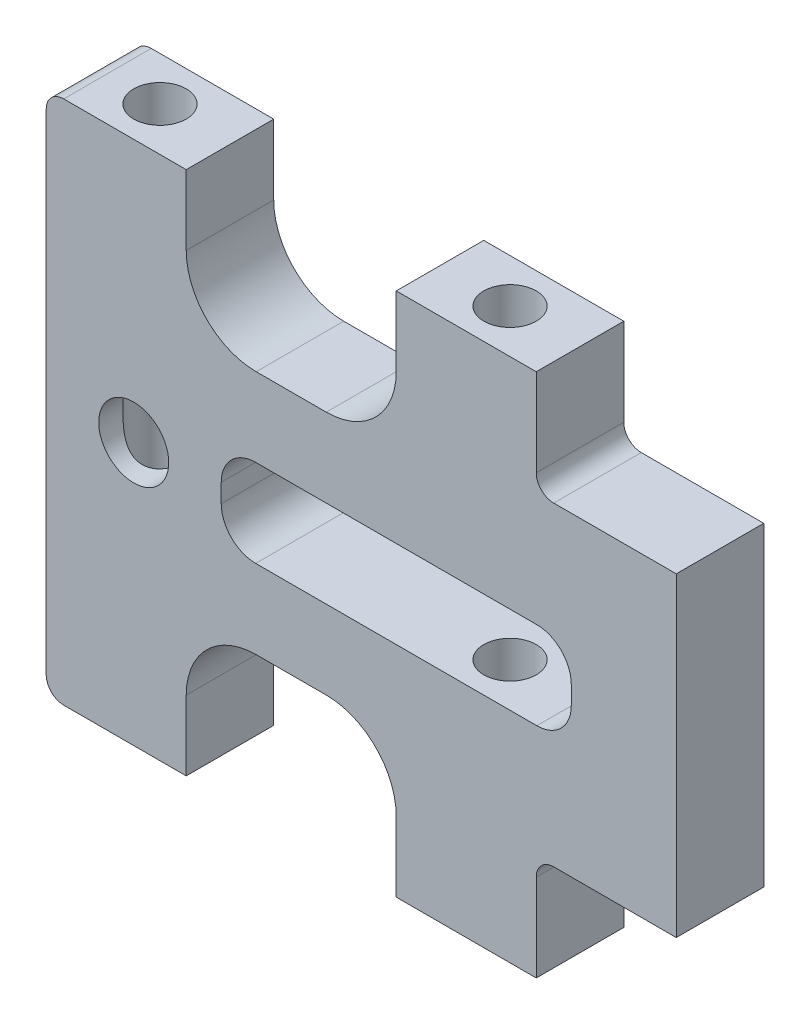
SolidWorks part; units mm, degrees
ref_plane "Front Plane" through (0, 0, 0) normal (0, 0, 1) x (1, 0, 0)
ref_plane "Top Plane" through (0, 0, 0) normal (0, 1, 0) x (1, 0, 0)
ref_plane "Right Plane" through (0, 0, 0) normal (1, 0, 0) x (0, 0, -1)
sketch "Sketch1" plane through (0, 0, 0) normal (0, 0, 1) x (1, 0, 0)
  line L1 (1, 0) -> (35, 0)
  line L2 (0, 1) -> (0, 7)
  line L3 (1, 30) -> (35, 30)
  line L4 (36, 1) -> (36, 29)
  line L7 (0, 7) -> (0, 29)
  line L9 (11.9675, 12.5) -> (28.0325, 12.5)
  line L10 (10, 14.4675) -> (10, 15.5325)
  line L11 (11.9675, 17.5) -> (28.0325, 17.5)
  line L12 (30, 14.4675) -> (30, 15.5325)
  line L13 (10, 12.5) -> (30, 17.5) construction
  line L14 (10, 17.5) -> (30, 12.5) construction
  circle A2 centre (5, 15) radius 2
  arc A3 (30, 15.5325) -> (28.0325, 17.5) centre (28.0325, 15.5325) ccw
  arc A4 (30, 14.4675) -> (28.0325, 12.5) centre (28.0325, 14.4675) cw
  arc A5 (10, 14.4675) -> (11.9675, 12.5) centre (11.9675, 14.4675) ccw
  arc A6 (10, 15.5325) -> (11.9675, 17.5) centre (11.9675, 15.5325) cw
  arc A7 (36, 29) -> (35, 30) centre (35, 29) ccw
  arc A8 (35, 0) -> (36, 1) centre (35, 1) ccw
  arc A10 (1, 0) -> (0, 1) centre (1, 1) cw
  arc A12 (0, 29) -> (1, 30) centre (1, 29) cw
  point P5 (0, 0)
  point P13 (10, 8)
  point P16 (20, 15)
  point P21 (0, 0)
  point P40 (0, 8)
  point P43 (0, 0)
  point P46 (0, 22)
  dimension "D6" = 5
  dimension "D8" = 1.9675
  dimension "D9" = 1
  dimension "D3" = 10
  dimension "D7" = 5
  dimension "D10" = 15
  dimension "D11" = 30
  dimension "D12" = 36
extrude "Boss-Extrude1" add sketch "Sketch1" along normal blind 5
sketch "Sketch2" plane through (0, 30, 0) normal (0, 1, 0) x (1, 0, 0)
  line L0 (0, -5) -> (0, 0) construction
  circle A0 centre (4, -2.5) radius 1.5
  circle A1 centre (24, -2.5) radius 1.5
  dimension "D1" = 4
  dimension "D2" = 20
extrude "Cut-Extrude1" cut sketch "Sketch2" against normal through all
sketch "Sketch3" plane through (0, 0, 5) normal (0, 0, 1) x (1, 0, 0)
  line L0 (28, 30) -> (28, 25)
  line L1 (35, 30) -> (1, 30) construction
  line L3 (44, 23) -> (44, 7)
  line L4 (43, 6) -> (29, 6)
  line L5 (28, 5) -> (28, 0)
  line L6 (1, 0) -> (35, 0) construction
  line L7 (28, 30) -> (56.7553, 30)
  line L8 (56.7553, 30) -> (56.7553, 0)
  line L9 (56.7553, 0) -> (28, 0)
  line L10 (43, 24) -> (29, 24)
  line L11 (8, 30) -> (8, 26)
  line L12 (12, 22) -> (16, 22)
  line L13 (20, 26) -> (20, 30)
  line L14 (0, 29) -> (0, 1) construction
  line L15 (8, 30) -> (20, 30)
  line L16 (0, 29) -> (0, 1) construction
  line L17 (8, 0) -> (8, 4)
  line L18 (12, 8) -> (16, 8)
  line L19 (20, 4) -> (20, 0)
  line L20 (8, 0) -> (20, 0)
  arc A0 (28, 25) -> (29, 24) centre (29, 25) ccw
  arc A1 (44, 23) -> (43, 24) centre (43, 23) ccw
  arc A2 (43, 6) -> (44, 7) centre (43, 7) ccw
  arc A3 (28, 5) -> (29, 6) centre (29, 5) cw
  arc A4 (16, 8) -> (20, 4) centre (16, 4) cw
  arc A5 (12, 8) -> (8, 4) centre (12, 4) ccw
  arc A6 (20, 26) -> (16, 22) centre (16, 26) cw
  arc A7 (12, 22) -> (8, 26) centre (12, 26) cw
  point P14 (28, 24)
  point P19 (44, 6)
  point P22 (28, 6)
  point P39 (8, 8)
  point P42 (20, 22)
  point P45 (8, 22)
  dimension "D4" = 1
  dimension "D11" = 4
  dimension "D1" = 6
  dimension "D2" = 6
  dimension "D3" = 16
  dimension "D5" = 8
  dimension "D6" = 12
  dimension "D7" = 28
  dimension "D8" = 28
  dimension "D9" = 8
  dimension "D10" = 8
extrude "Cut-Extrude2" cut sketch "Sketch3" against normal through all
